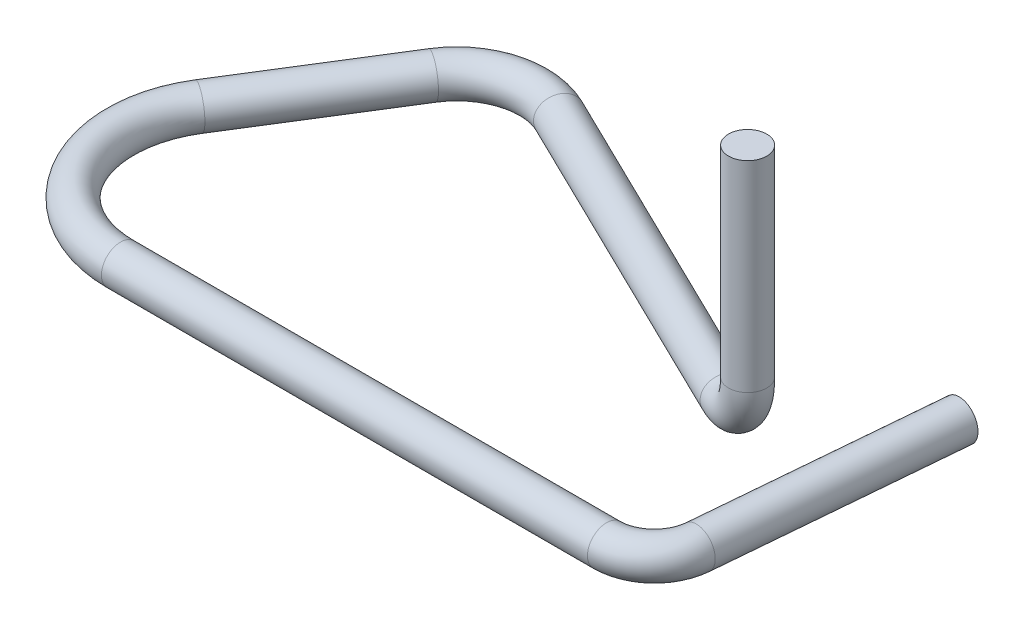
SolidWorks part; units mm, degrees
ref_plane "Front" through (0, 0, 0) normal (0, 0, 1) x (1, 0, 0)
ref_plane "Top" through (0, 0, 0) normal (0, 1, 0) x (1, 0, 0)
ref_plane "Right" through (0, 0, 0) normal (1, 0, 0) x (0, 0, -1)
sketch "Sketch1" plane through (0, 0, 0) normal (0, 1, 0) x (1, 0, 0)
  line L0 (16.4634, 0.508) -> (3.556, 0.508)
  line L1 (0.9711, 5.1712) -> (3.3568, 8.989)
  line L2 (5.9708, 9.7385) -> (15.748, 4.9699) construction
  line L3 (0.508, 3.556) -> (0.508, 0.7447) construction
  line L4 (0.508, 3.556) -> (0.508, 7.7927) construction
  line L5 (17.7286, 1.6673) -> (18.2899, 8.0837)
  line L6 (17.7839, 8.128) -> (18.796, 8.0394) construction
  line L7 (5.9708, 9.7385) -> (14.6065, 5.5266)
  arc A0 (3.556, 0.508) -> (0.9711, 5.1712) centre (3.556, 3.556) cw
  arc A1 (3.3568, 8.989) -> (5.9708, 9.7385) centre (5.08, 7.9122) cw
  arc A2 (17.7286, 1.6673) -> (16.4634, 0.508) centre (16.4634, 1.778) cw
  point P17 (18.2899, 8.0837)
  dimension "D2" = 3.048
  dimension "D5" = 2.032
  dimension "D10" = 1.27
  dimension "D1" = 0.508
  dimension "D3" = 0.508
  dimension "D4" = 32
  dimension "D6" = 96
  dimension "D7" = 4.572
  dimension "D8" = 7.9122
  dimension "D9" = 95
  dimension "D11" = 1.016
  dimension "D12" = 8.128
  dimension "D13" = 18.288
  dimension "D14" = 15.24
  dimension "D15" = 1.27
ref_plane "Plane1" through (15.748, 0, 0) normal (1, 0, 0) x (0, 0, -1)
sketch "Sketch2" plane through (15.748, 0, 0) normal (1, 0, 0) x (0, 0, -1)
  line L0 (4.9699, 0) -> (4.9699, 6.604) construction
  dimension "D1" = 6.604
ref_plane "Plane2" through (4.9844, 0, -10.2196) normal (0.4384, 0, -0.8988) x (-0.8988, 0, -0.4384)
sketch "Sketch3" plane through (4.9844, 0, -10.2196) normal (0.4384, 0, -0.8988) x (-0.8988, 0, -0.4384)
  line L0 (-11.9756, 6.604) -> (-11.9756, 1.27)
  line L1 (-1.0974, 0) -> (-10.7056, 0) construction
  line L2 (-11.9756, 0) -> (-11.9756, 6.604) construction
  line L3 (-1.0974, 0) -> (-10.7056, 0) construction
  arc A0 (-11.9756, 1.27) -> (-10.7056, 0) centre (-10.7056, 1.27) ccw
ref_plane "Plane3" through (0, 6.604, 0) normal (0, 1, 0) x (1, 0, 0)
sketch "Sketch4" plane through (0, 6.604, 0) normal (0, 1, 0) x (1, 0, 0)
  circle A0 centre (15.748, 4.9699) radius 0.508
  dimension "D1" = 1.016
curve "CompCurve1"
sweep "Sweep1" add profiles "Sketch4" path "CompCurve1"
